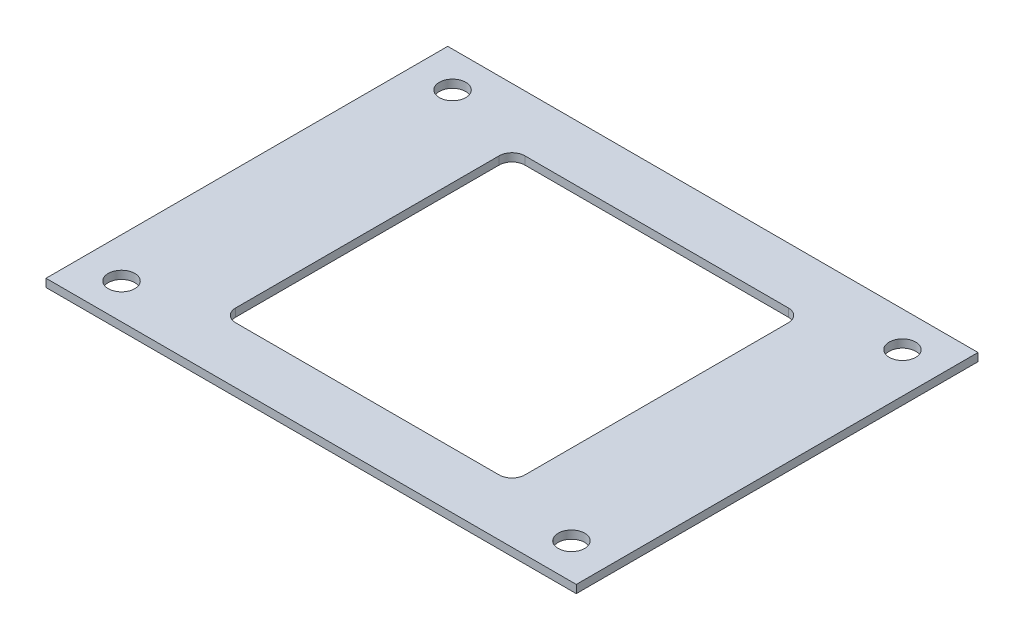
SolidWorks part; units mm, degrees
ref_plane "Front Plane" through (0, 0, 0) normal (0, 0, 1) x (1, 0, 0)
ref_plane "Top Plane" through (0, 0, 0) normal (0, 1, 0) x (1, 0, 0)
ref_plane "Right Plane" through (0, 0, 0) normal (1, 0, 0) x (0, 0, -1)
sketch "Sketch1" plane through (0, 0, 0) normal (0, 1, 0) x (1, 0, 0)
  line L1 (-33, -25) -> (33, -25)
  line L2 (-33, -25) -> (-33, 25)
  line L3 (-33, 25) -> (33, 25)
  line L4 (33, -25) -> (33, 25)
  line L5 (-33, -25) -> (33, 25) construction
  line L6 (-33, 25) -> (33, -25) construction
  line L7 (-18, -18) -> (18, -18)
  line L8 (-18, -18) -> (-18, 18)
  line L9 (-18, 18) -> (18, 18)
  line L10 (18, -18) -> (18, 18)
  line L11 (-18, -18) -> (18, 18) construction
  line L12 (-18, 18) -> (18, -18) construction
  circle A0 centre (-28, 20.6) radius 1.65
  circle A1 centre (-28, -20.6) radius 1.65
  circle A2 centre (28, 20.6) radius 1.65
  circle A3 centre (28, -20.6) radius 1.65
  point P0 (0, 0)
  point P5 (0, 0)
  dimension "D5" = 2.6
  dimension "D6" = 2.6
  dimension "D7" = 10
  dimension "D8" = 10
  dimension "D9" = 3.3
  dimension "D10" = 3.3
  dimension "D11" = 2.6
  dimension "D12" = 2.6
  dimension "D13" = 10
  dimension "D15" = 3.3
  dimension "D16" = 3.3
  dimension "D1" = 66
  dimension "D2" = 50
  dimension "D3" = 36
  dimension "D4" = 36
  dimension "D14" = 10
extrude "Boss-Extrude1" add sketch "Sketch1" along normal blind 1
fillet "Fillet1" radius 1.6 4 edges at (-18, 0.5, 18) (18, 0.5, 18) (18, 0.5, -18) (-18, 0.5, -18)
